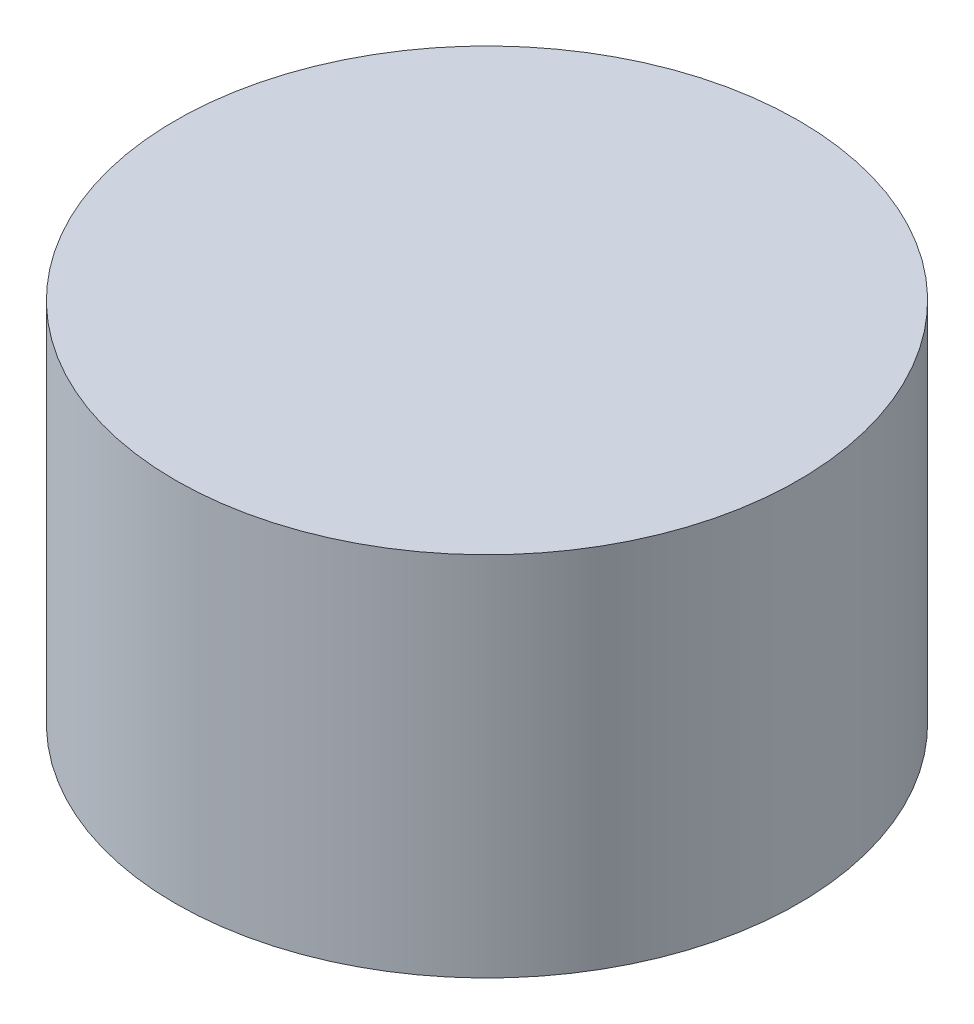
SolidWorks part; units mm, degrees
ref_plane "Front Plane" through (0, 0, 0) normal (0, 0, 1) x (1, 0, 0)
ref_plane "Top Plane" through (0, 0, 0) normal (0, 1, 0) x (1, 0, 0)
ref_plane "Right Plane" through (0, 0, 0) normal (1, 0, 0) x (0, 0, -1)
sketch "Sketch1" plane through (0, 0, 0) normal (0, 1, 0) x (1, 0, 0)
  circle A0 centre (-2.573, 1.5743) radius 8.5
  dimension "D1" = 17
extrude "Boss-Extrude1" add sketch "Sketch1" along normal blind 10 contours A0
